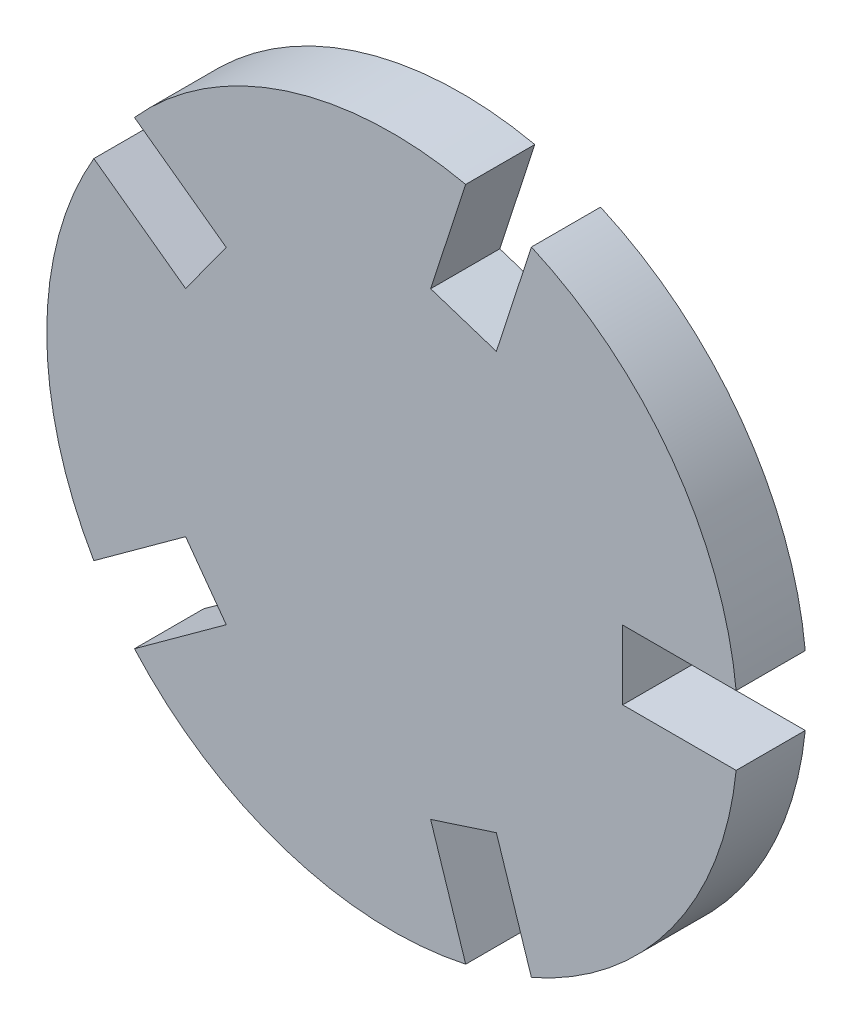
SolidWorks part; units mm, degrees
ref_plane "Alzado" through (0, 0, 0) normal (0, 0, 1) x (1, 0, 0)
ref_plane "Planta" through (0, 0, 0) normal (0, 1, 0) x (1, 0, 0)
ref_plane "Vista lateral" through (0, 0, 0) normal (1, 0, 0) x (0, 0, -1)
sketch "Croquis1" plane through (0, 0, 0) normal (0, 0, 1) x (1, 0, 0)
  line L0 (0, 0) -> (15, 0) construction
  line L1 (10, -1.5) -> (20, -1.5)
  line L2 (10, -1.5) -> (10, 1.5)
  line L3 (10, 1.5) -> (20, 1.5)
  line L4 (20, -1.5) -> (20, 1.5)
  line L5 (10, -1.5) -> (20, 1.5) construction
  line L6 (10, 1.5) -> (15, 0) construction
  line L7 (15, 0) -> (20, -1.5) construction
  line L8 (1.6636, -9.9741) -> (4.7538, -19.4847)
  line L9 (4.5168, -9.047) -> (7.6069, -18.5576)
  line L10 (4.7538, -19.4847) -> (7.6069, -18.5576)
  line L11 (1.6636, -9.9741) -> (7.6069, -18.5576) construction
  line L12 (4.5168, -9.047) -> (4.6353, -14.2658) construction
  line L13 (4.6353, -14.2658) -> (4.7538, -19.4847) construction
  line L14 (1.6636, -9.9741) -> (4.5168, -9.047)
  line L15 (-8.9718, -4.6643) -> (-17.062, -10.5422)
  line L16 (-7.2085, -7.0914) -> (-15.2987, -12.9692)
  line L17 (-17.062, -10.5422) -> (-15.2987, -12.9692)
  line L18 (-8.9718, -4.6643) -> (-15.2987, -12.9692) construction
  line L19 (-7.2085, -7.0914) -> (-12.1353, -8.8168) construction
  line L20 (-12.1353, -8.8168) -> (-17.062, -10.5422) construction
  line L21 (-8.9718, -4.6643) -> (-7.2085, -7.0914)
  line L22 (-7.2085, 7.0914) -> (-15.2987, 12.9692)
  line L23 (-8.9718, 4.6643) -> (-17.062, 10.5422)
  line L24 (-15.2987, 12.9692) -> (-17.062, 10.5422)
  line L25 (-7.2085, 7.0914) -> (-17.062, 10.5422) construction
  line L26 (-8.9718, 4.6643) -> (-12.1353, 8.8168) construction
  line L27 (-12.1353, 8.8168) -> (-15.2987, 12.9692) construction
  line L28 (-7.2085, 7.0914) -> (-8.9718, 4.6643)
  line L29 (4.5168, 9.047) -> (7.6069, 18.5576)
  line L30 (1.6636, 9.9741) -> (4.7538, 19.4847)
  line L31 (7.6069, 18.5576) -> (4.7538, 19.4847)
  line L32 (4.5168, 9.047) -> (4.7538, 19.4847) construction
  line L33 (1.6636, 9.9741) -> (4.6353, 14.2658) construction
  line L34 (4.6353, 14.2658) -> (7.6069, 18.5576) construction
  line L35 (4.5168, 9.047) -> (1.6636, 9.9741)
  circle A0 centre (0, 0) radius 15
  point P3 (15, 0)
  point P11 (4.6353, -14.2658)
  point P17 (-12.1353, -8.8168)
  point P23 (-12.1353, 8.8168)
  point P29 (4.6353, 14.2658)
  point P35 (0, 0)
  dimension "D1" = 30
  dimension "D2" = 3
  dimension "D3" = 10
  dimension "D4" = 5
extrude "Saliente-Extruir1" add sketch "Croquis1" along normal blind 3
equation "\"A\"= 10"
equation "\"B\"= 3"
equation "\"D3@Croquis1\"=\"A\""
equation "\"D1@Croquis1\"=\"A\"*3"
equation "\"D2@Croquis1\"=\"B\""
